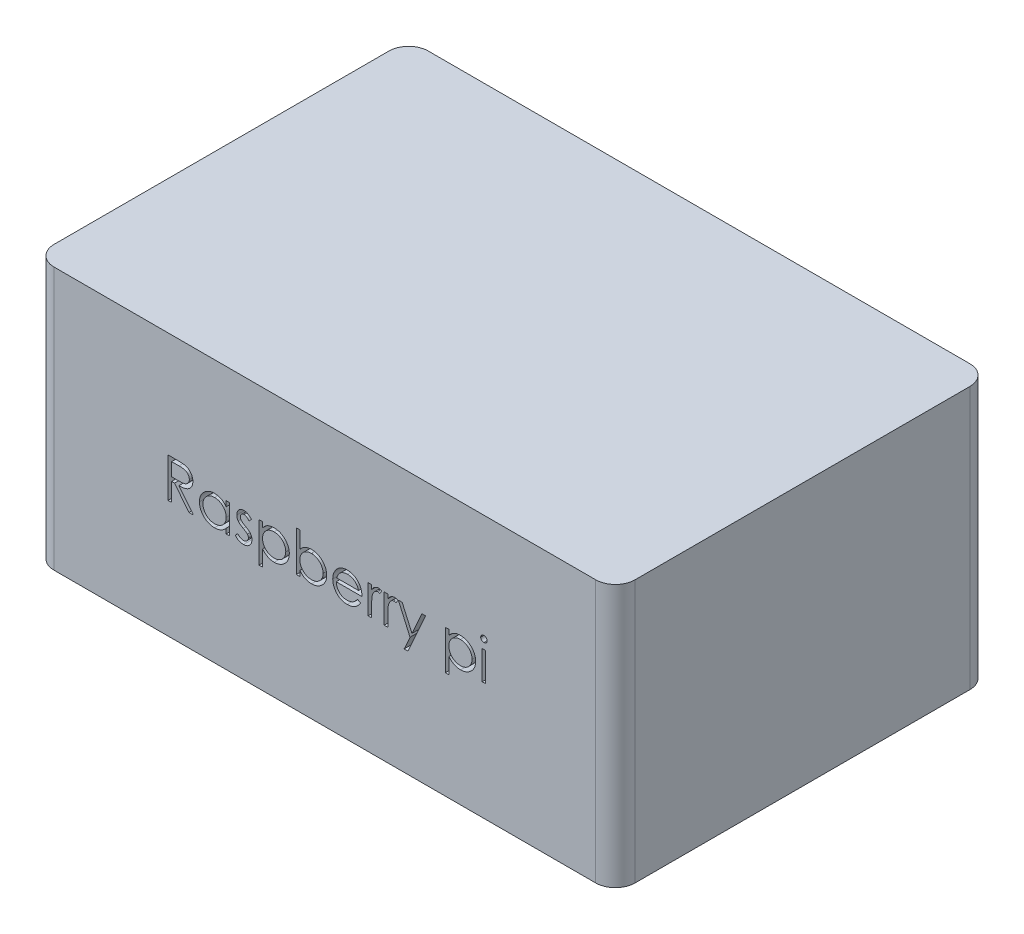
SolidWorks part; units mm, degrees
ref_plane "Alzado" through (0, 0, 0) normal (0, 0, 1) x (1, 0, 0)
ref_plane "Planta" through (0, 0, 0) normal (0, 1, 0) x (1, 0, 0)
ref_plane "Vista lateral" through (0, 0, 0) normal (1, 0, 0) x (0, 0, -1)
sketch "Croquis1" plane through (0, 0, 0) normal (0, 1, 0) x (1, 0, 0)
  line L1 (-59.1994, 39.3876) -> (29.3006, 39.3876)
  line L2 (-59.1994, 39.3876) -> (-59.1994, -17.6124)
  line L3 (-59.1994, -17.6124) -> (29.3006, -17.6124)
  line L4 (29.3006, 39.3876) -> (29.3006, -17.6124)
  dimension "D1" = 57
  dimension "D2" = 88.5
extrude "Saliente-Extruir1" add sketch "Croquis1" along normal blind 40
sketch "Croquis2" plane through (0, 0, 17.6124) normal (0, 0, 1) x (1, 0, 0)
  text T0 "Raspberry pi\r\n" font "Century Gothic" height 6
extrude "Cortar-Extruir1" cut sketch "Croquis2" against normal blind 4
fillet "Redondeo1" radius 3 4 edges at (29.3006, 20, 17.6124) (29.3006, 20, -39.3876) (-59.1994, 20, -39.3876) (-59.1994, 20, 17.6124)
